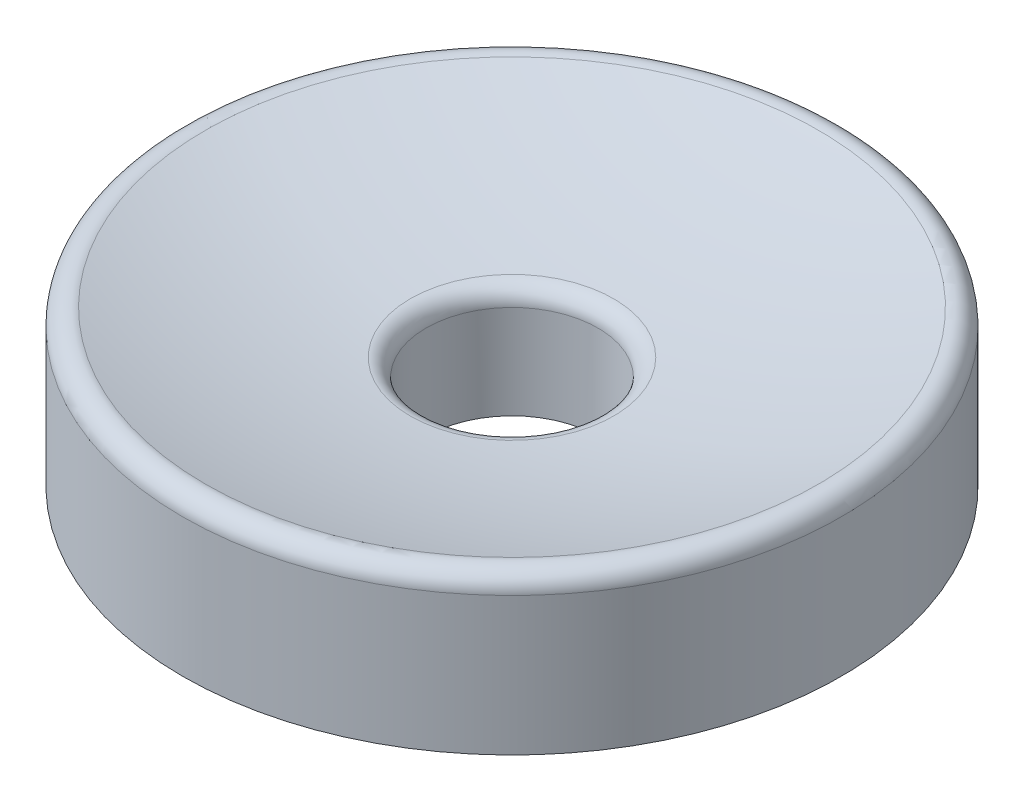
SolidWorks part; units mm, degrees
material "6061-T6 Al"
ref_plane "Front Plane" through (0, 0, 0) normal (0, 0, 1) x (1, 0, 0)
ref_plane "Top Plane" through (0, 0, 0) normal (0, 1, 0) x (1, 0, 0)
ref_plane "Right Plane" through (0, 0, 0) normal (1, 0, 0) x (0, 0, -1)
sketch "Sketch1" plane through (0, 0, 0) normal (0, 0, 1) x (1, 0, 0)
  line L0 (0, 0) -> (0, -53.4359) construction
  line L2 (4.9657, -63.2839) -> (19.05, -63.2839)
  line L3 (19.05, -63.2839) -> (19.05, -53.8815)
  line L4 (4.9657, -56.9339) -> (4.9657, -63.2839)
  arc A0 (4.9657, -56.9339) -> (19.05, -53.8815) centre (0, 0) ccw
  dimension "D1" = 57.15
  dimension "D2" = 9.9314
  dimension "D3" = 38.1
  dimension "D4" = 6.35
revolve "Revolve1" add sketch "Sketch1" angle 360 about L0
fillet "Fillet1" radius 1.016 1 edges at (0, -53.8815, 19.05)
fillet "Fillet2" radius 1.016 1 edges at (0, -56.9339, 4.9657)
